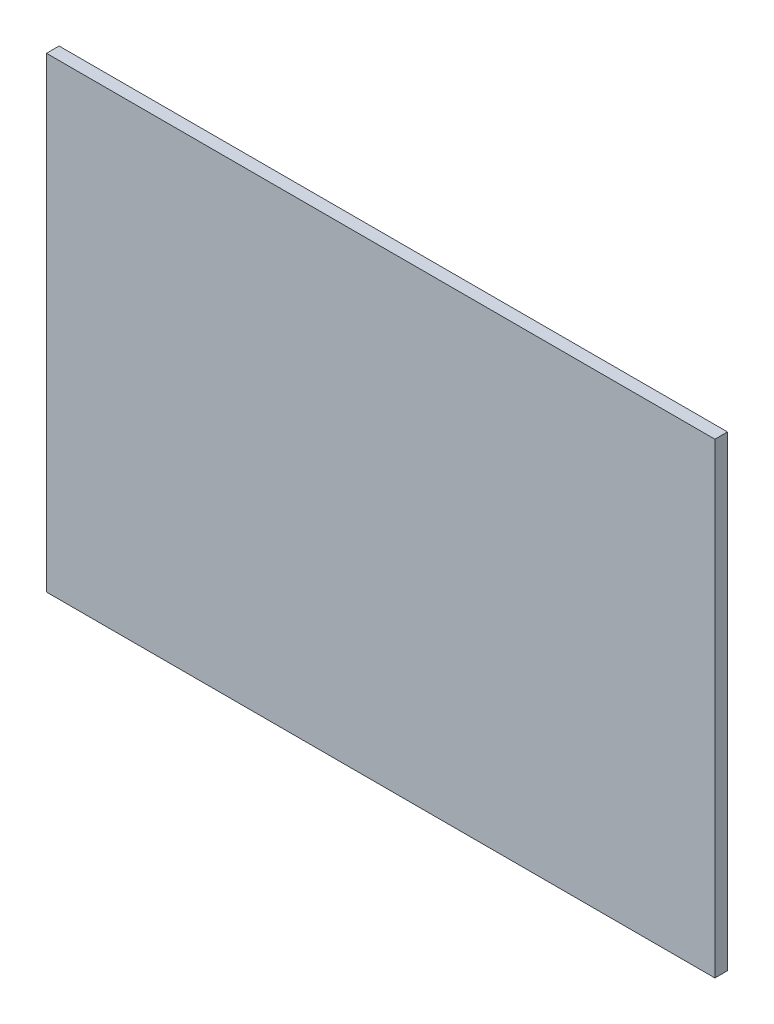
SolidWorks part; units mm, degrees
ref_plane "Ön Düzlem" through (0, 0, 0) normal (0, 0, 1) x (1, 0, 0)
ref_plane "Üst Düzlem" through (0, 0, 0) normal (0, 1, 0) x (1, 0, 0)
ref_plane "Sağ Düzlem" through (0, 0, 0) normal (1, 0, 0) x (0, 0, -1)
sketch "Sketch1" plane through (0, 0, 0) normal (0, 0, 1) x (1, 0, 0)
  line L1 (-265, -185) -> (265, -185)
  line L2 (-265, -185) -> (-265, 185)
  line L3 (-265, 185) -> (265, 185)
  line L4 (265, -185) -> (265, 185)
  line L5 (-265, -185) -> (265, 185) construction
  line L6 (-265, 185) -> (265, -185) construction
  point P0 (0, 0)
  dimension "D1" = 530
  dimension "D2" = 370
extrude "Boss-Extrude1" add sketch "Sketch1" along normal blind 10
